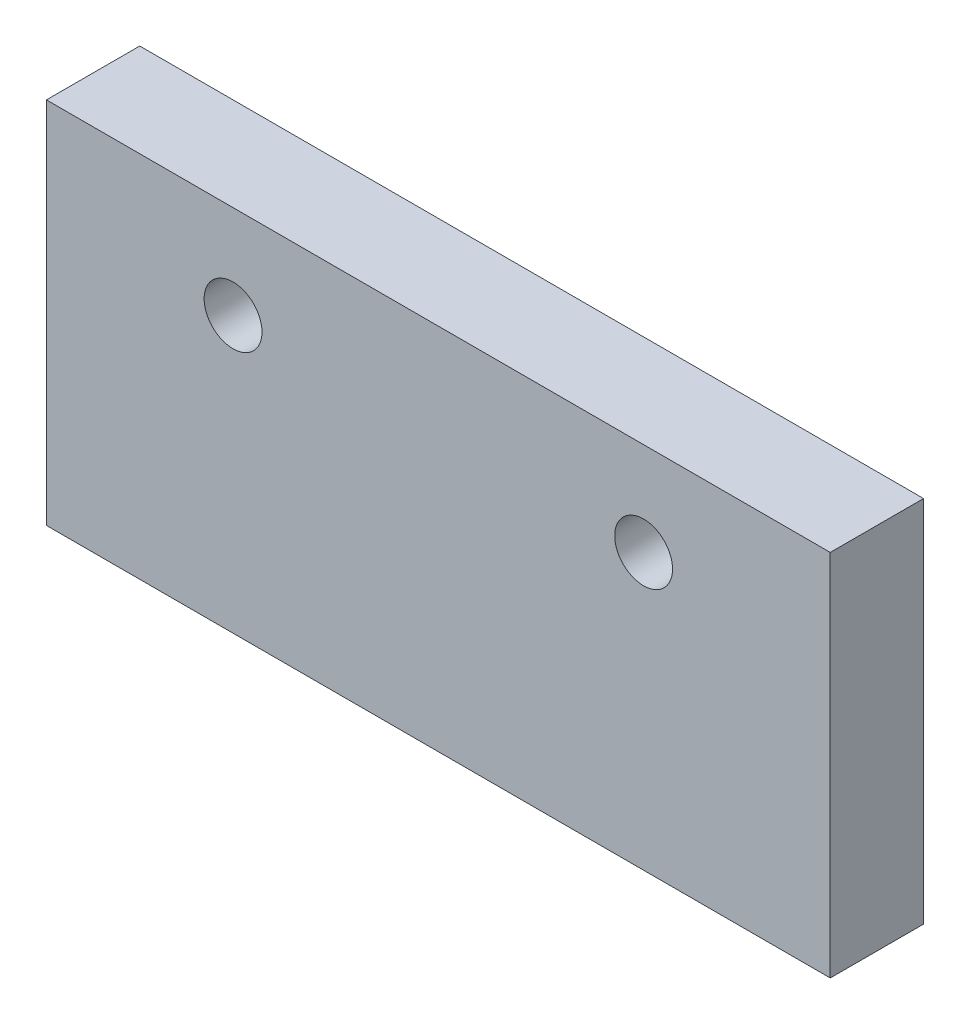
SolidWorks part; units mm, degrees
ref_plane "前视基准面" through (0, 0, 0) normal (0, 0, 1) x (1, 0, 0)
ref_plane "上视基准面" through (0, 0, 0) normal (0, 1, 0) x (1, 0, 0)
ref_plane "右视基准面" through (0, 0, 0) normal (1, 0, 0) x (0, 0, -1)
sketch "草图1" plane through (0, 0, 0) normal (0, 0, 1) x (1, 0, 0)
  line L0 (0, 17) -> (0, 7)
  line L2 (0, 0) -> (0, 17)
  line L3 (0, 17) -> (42, 17)
  line L4 (42, 0) -> (42, 17)
  line L6 (0, 0) -> (0, -2.75)
  line L7 (0, -2.75) -> (42, -2.75)
  line L8 (42, 0) -> (42, -2.75)
  line L9 (0, 17) -> (0, 0)
  line L10 (0, 0) -> (0, -2.75)
  line L12 (42, 17) -> (42, 7)
  circle A0 centre (10, 12) radius 1.55
  circle A1 centre (32, 12) radius 1.55
extrude "凸台-拉伸1" add sketch "草图1" along normal blind 5 contours L8 L4 L3 L0 L2 L6 L7 A1 A0
